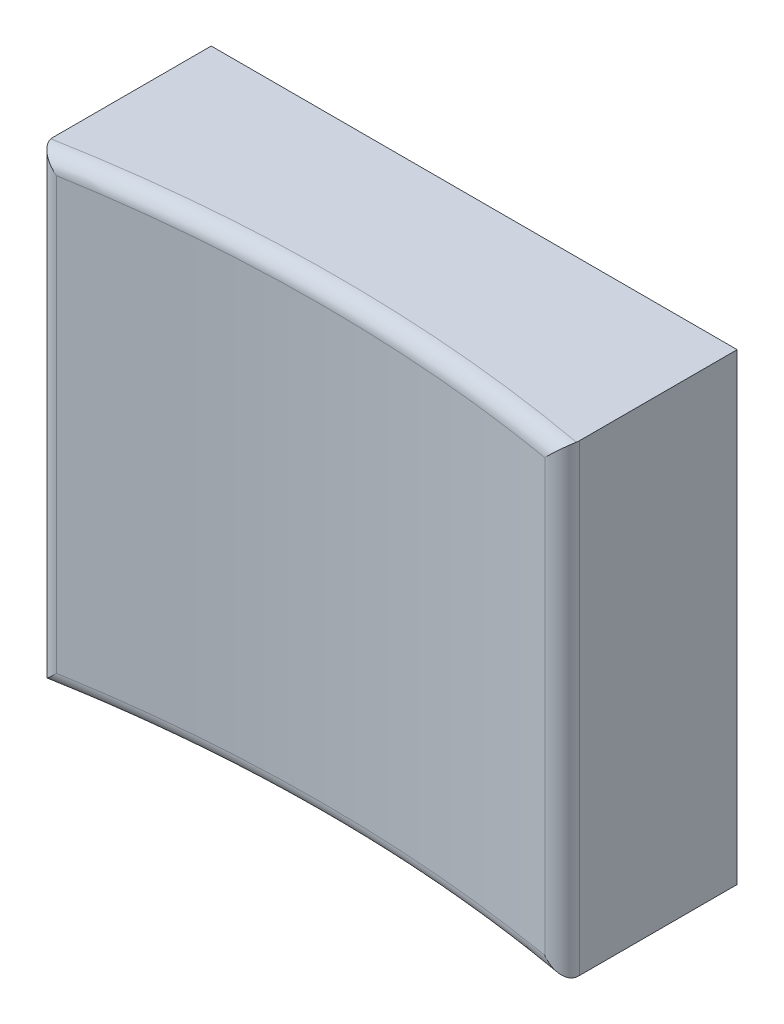
SolidWorks part; units mm, degrees
ref_plane "Front" through (0, 0, 0) normal (0, 0, 1) x (1, 0, 0)
ref_plane "Top" through (0, 0, 0) normal (0, 1, 0) x (1, 0, 0)
ref_plane "Right" through (0, 0, 0) normal (1, 0, 0) x (0, 0, -1)
sketch "Sketch1" plane through (0, 0, 0) normal (0, 0, 1) x (1, 0, 0)
  line L0 (-4.1529, 0) -> (4.1529, 0) construction
  line L1 (-4.1529, 3.6576) -> (4.1529, 3.6576)
  line L2 (-4.1529, 3.6576) -> (-4.1529, -3.6576)
  line L3 (-4.1529, -3.6576) -> (4.1529, -3.6576)
  line L4 (4.1529, 3.6576) -> (4.1529, -3.6576)
  point P6 (0, 0)
  dimension "D1" = 8.3058
  dimension "D2" = 7.3152
extrude "key" add sketch "Sketch1" along normal blind 2.794
sketch "Sketch2" plane through (0, -3.6576, 0) normal (0, -1, 0) x (1, 0, 0)
  arc A0 (-4.1529, 2.794) -> (4.1529, 2.794) centre (0, 25.2736) ccw
  line M4 (4.1529, 2.794) -> (-4.1529, 2.794)
  dimension "D1" = 22.86
extrude "Extrude2" cut sketch "Sketch2" against normal through all contours A0 M4
fillet "Fillet1" radius 0.254 4 edges at (0, -3.6576, 2.4136) (4.1529, 0, 2.794) (0, 3.6576, 2.4136) (-4.1529, 0, 2.794)
